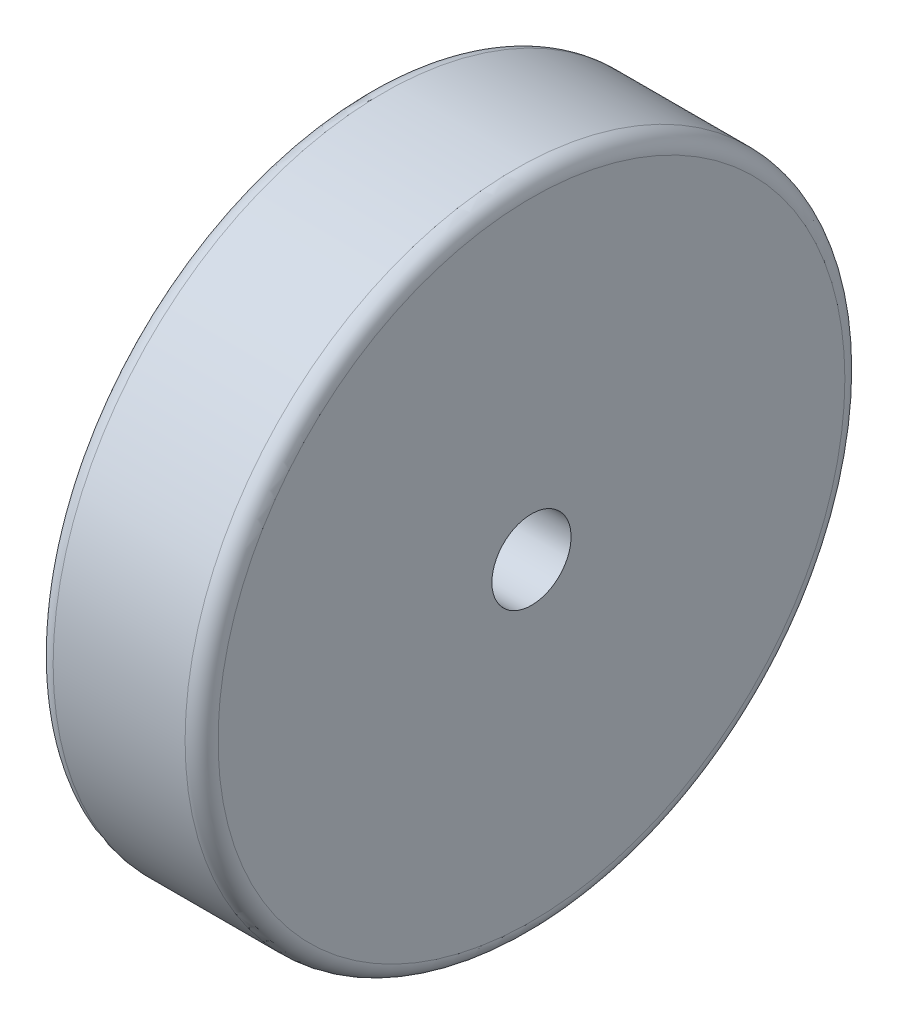
SolidWorks part; units mm, degrees
ref_plane "Front Plane" through (0, 0, 0) normal (0, 0, 1) x (1, 0, 0)
ref_plane "Top Plane" through (0, 0, 0) normal (0, 1, 0) x (1, 0, 0)
ref_plane "Right Plane" through (0, 0, 0) normal (1, 0, 0) x (0, 0, -1)
sketch "Sketch2" plane through (0, 0, 0) normal (1, 0, 0) x (0, 0, -1)
  circle A0 centre (0, 0) radius 50
  dimension "D1" = 100
extrude "Boss-Extrude1" add sketch "Sketch2" against normal blind 25
fillet "Fillet1" radius 2.5 2 edges at (0, 0, -50) (-25, 0, -50)
sketch "Sketch3" plane through (-25, 0, 0) normal (-1, 0, 0) x (0, 0, 1)
  circle A0 centre (0, 0) radius 6
  dimension "D1" = 12
extrude "Cut-Extrude1" cut sketch "Sketch3" against normal blind 25
